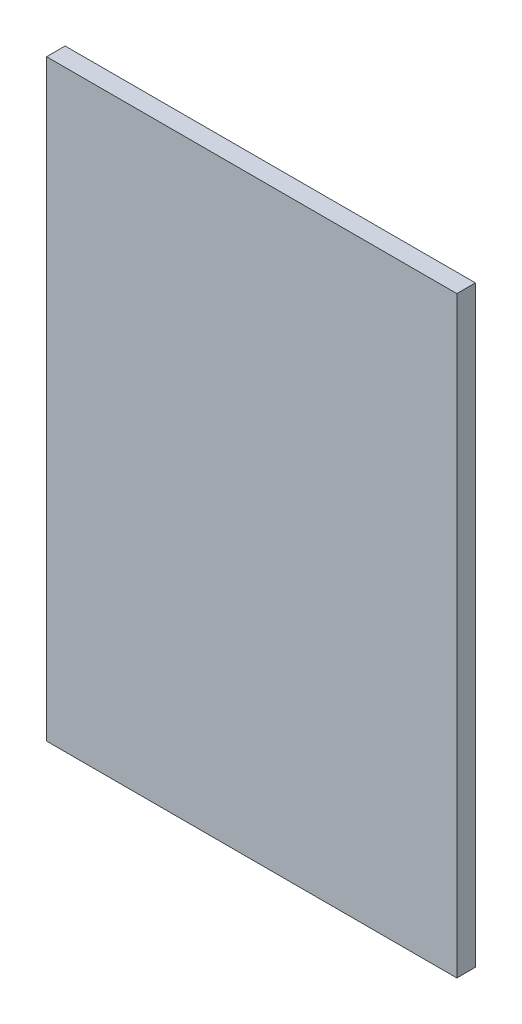
SolidWorks part; units mm, degrees
ref_plane "Front Plane" through (0, 0, 0) normal (0, 0, 1) x (1, 0, 0)
ref_plane "Top Plane" through (0, 0, 0) normal (0, 1, 0) x (1, 0, 0)
ref_plane "Right Plane" through (0, 0, 0) normal (1, 0, 0) x (0, 0, -1)
sketch "Sketch1" plane through (0, 0, 0) normal (0, 0, 1) x (1, 0, 0)
  line L1 (199, -287.5) -> (-199, -287.5)
  line L2 (199, -287.5) -> (199, 287.5)
  line L3 (199, 287.5) -> (-199, 287.5)
  line L4 (-199, -287.5) -> (-199, 287.5)
  line L5 (199, -287.5) -> (-199, 287.5) construction
  line L6 (199, 287.5) -> (-199, -287.5) construction
  point P0 (0, 0)
  dimension "D1" = 575
  dimension "D2" = 398
extrude "Boss-Extrude1" add sketch "Sketch1" along normal blind 18
equation "\"H_DSP\"=18"
equation "\"D1@Boss-Extrude1\"=\"H_DSP\""
